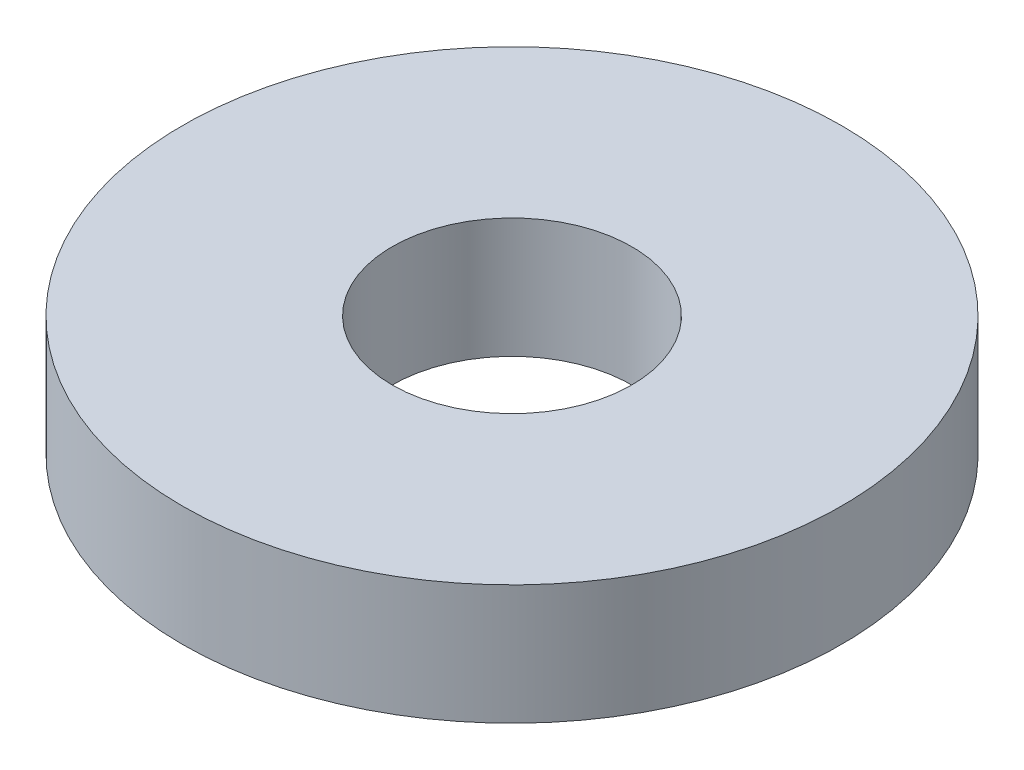
SolidWorks part; units mm, degrees
ref_plane "Front Plane" through (0, 0, 0) normal (0, 0, 1) x (1, 0, 0)
ref_plane "Top Plane" through (0, 0, 0) normal (0, 1, 0) x (1, 0, 0)
ref_plane "Right Plane" through (0, 0, 0) normal (1, 0, 0) x (0, 0, -1)
sketch "Sketch1" plane through (0, 0, 0) normal (0, 1, 0) x (1, 0, 0)
  circle A0 centre (0, 0) radius 27.5
  circle A1 centre (0, 0) radius 10
  dimension "D1" = 55
  dimension "D2" = 20
extrude "Boss-Extrude1" add sketch "Sketch1" along normal blind 10
